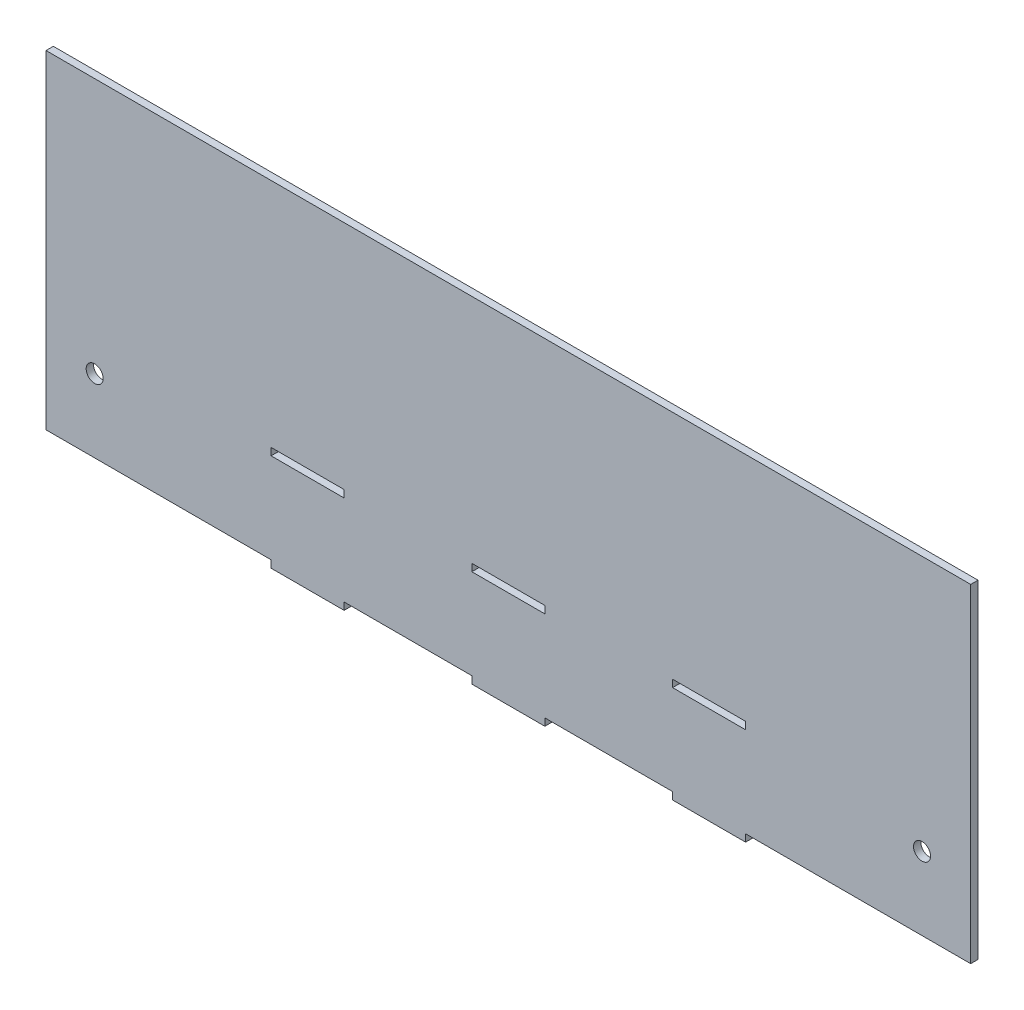
SolidWorks part; units mm, degrees
ref_plane "Alzado" through (0, 0, 0) normal (0, 0, 1) x (1, 0, 0)
ref_plane "Planta" through (0, 0, 0) normal (0, 1, 0) x (1, 0, 0)
ref_plane "Vista lateral" through (0, 0, 0) normal (1, 0, 0) x (0, 0, -1)
sketch "Croquis1" plane through (0, 0, 0) normal (0, 0, 1) x (1, 0, 0)
  line L0 (-190, -27.5) -> (190, -27.5) construction
  line L1 (-190, -67.5) -> (-97.5, -67.5)
  line L2 (-190, -67.5) -> (-190, 67.5)
  line L3 (-190, 67.5) -> (190, 67.5)
  line L4 (190, -67.5) -> (190, 67.5)
  line L5 (-190, -67.5) -> (190, 67.5) construction
  line L6 (-190, 67.5) -> (190, -67.5) construction
  line L7 (67.5, -30.5) -> (97.5, -30.5)
  line L8 (-15, -30.5) -> (15, -30.5)
  line L9 (-15, -30.5) -> (-15, -27.5)
  line L10 (-15, -27.5) -> (15, -27.5)
  line L11 (15, -30.5) -> (15, -27.5)
  line L12 (-15, -30.5) -> (15, -27.5) construction
  line L13 (-15, -27.5) -> (15, -30.5) construction
  line L14 (67.5, -30.5) -> (67.5, -27.5)
  line L15 (67.5, -27.5) -> (97.5, -27.5)
  line L16 (97.5, -30.5) -> (97.5, -27.5)
  line L17 (67.5, -30.5) -> (97.5, -27.5) construction
  line L18 (67.5, -27.5) -> (97.5, -30.5) construction
  line L19 (-15, -70.5) -> (15, -70.5)
  line L20 (-15, -70.5) -> (-15, -67.5)
  line L22 (15, -70.5) -> (15, -67.5)
  line L23 (-15, -70.5) -> (15, -67.5) construction
  line L24 (-15, -67.5) -> (15, -70.5) construction
  line L25 (67.5, -70.5) -> (97.5, -70.5)
  line L26 (67.5, -70.5) -> (67.5, -67.5)
  line L28 (97.5, -70.5) -> (97.5, -67.5)
  line L29 (67.5, -70.5) -> (97.5, -67.5) construction
  line L30 (67.5, -67.5) -> (97.5, -70.5) construction
  line L31 (-97.5, -30.5) -> (-67.5, -30.5)
  line L32 (-97.5, -30.5) -> (-97.5, -27.5)
  line L33 (-97.5, -27.5) -> (-67.5, -27.5)
  line L34 (-67.5, -30.5) -> (-67.5, -27.5)
  line L35 (-97.5, -30.5) -> (-67.5, -27.5) construction
  line L36 (-97.5, -27.5) -> (-67.5, -30.5) construction
  line L37 (-97.5, -70.5) -> (-67.5, -70.5)
  line L38 (-97.5, -70.5) -> (-97.5, -67.5)
  line L40 (-67.5, -70.5) -> (-67.5, -67.5)
  line L41 (-97.5, -70.5) -> (-67.5, -67.5) construction
  line L42 (-97.5, -67.5) -> (-67.5, -70.5) construction
  line L43 (0, 67.5) -> (0, -70) construction
  line L44 (-67.5, -67.5) -> (-15, -67.5)
  line L45 (15, -67.5) -> (67.5, -67.5)
  line L46 (97.5, -67.5) -> (190, -67.5)
  circle A0 centre (-170, -37.5) radius 3.5
  circle A1 centre (170, -37.5) radius 3.5
  point P0 (0, 0)
  point P8 (0, -29)
  point P13 (82.5, -29)
  point P18 (0, -69)
  point P23 (82.5, -69)
  point P28 (-82.5, -29)
  point P33 (-82.5, -69)
  dimension "D18" = 7
  dimension "D21" = 7
  dimension "D1" = 380
  dimension "D2" = 135
  dimension "D3" = 40
  dimension "D4" = 3
  dimension "D5" = 30
  dimension "D6" = 3
  dimension "D7" = 30
  dimension "D8" = 3
  dimension "D9" = 30
  dimension "D10" = 3
  dimension "D11" = 30
  dimension "D12" = 3
  dimension "D13" = 30
  dimension "D14" = 3
  dimension "D15" = 30
  dimension "D16" = 82.5
  dimension "D17" = 82.5
  dimension "D19" = 30
  dimension "D20" = 20
  dimension "D22" = 30
  dimension "D23" = 20
extrude "Saliente-Extruir1" add sketch "Croquis1" along normal blind 3
